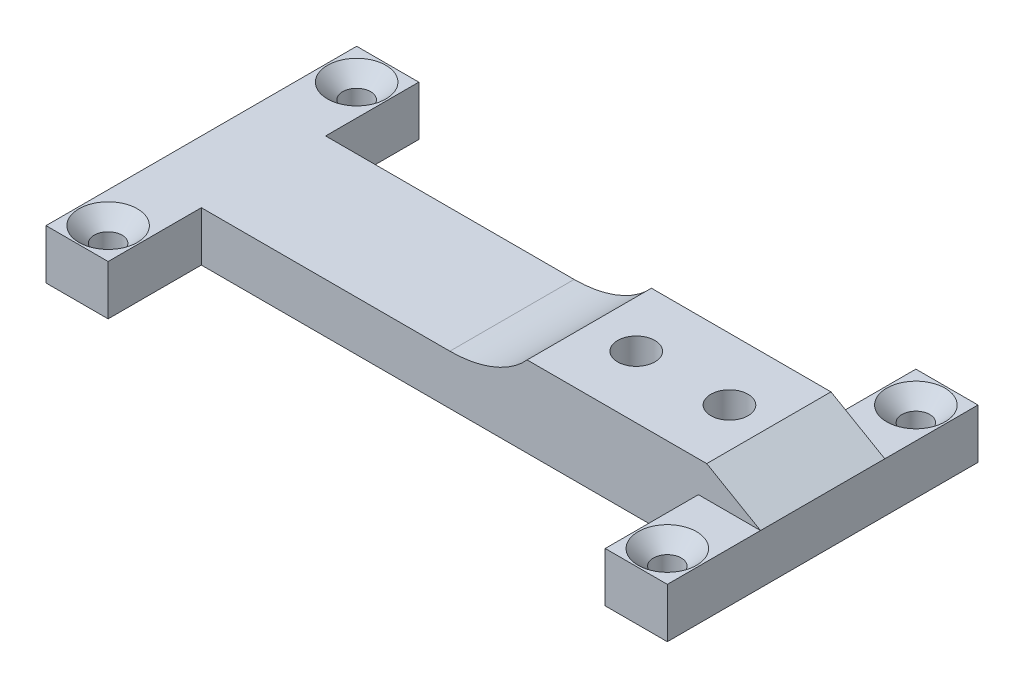
SolidWorks part; units mm, degrees
ref_plane "Front Plane" through (0, 0, 0) normal (0, 0, 1) x (1, 0, 0)
ref_plane "Top Plane" through (0, 0, 0) normal (0, 1, 0) x (1, 0, 0)
ref_plane "Right Plane" through (0, 0, 0) normal (1, 0, 0) x (0, 0, -1)
sketch "Sketch1" plane through (0, 0, 0) normal (0, 0, 1) x (1, 0, 0)
  line L0 (0, 0) -> (0, 6.35)
  line L1 (0, 6.35) -> (0, -6.35)
  line L2 (50, -11.35) -> (41.3397, -6.35)
  line L3 (0, -6.35) -> (40, -6.35)
  line L4 (0, -6.35) -> (0, 6.35)
  line L5 (0, 6.35) -> (40, 6.35)
  line L6 (40, -6.35) -> (40, 6.35)
  line L7 (0, -11.35) -> (50, -11.35)
  line L8 (0, -11.35) -> (0, -19.35)
  line L9 (0, -19.35) -> (50, -19.35)
  line L10 (50, -11.35) -> (50, -19.35)
  line L11 (40, -6.35) -> (41.3397, -6.35)
  line L12 (0, -19.35) -> (-50, -19.35)
  line L13 (0, -19.35) -> (0, -11.35)
  line L14 (0, -11.35) -> (-50, -11.35)
  line L15 (-50, -19.35) -> (-50, -11.35)
  ellipse E0 centre (0, 0) end of major axis (-15, 0) minor radius 11.35
  dimension "D1" = 6.35
  dimension "D2" = 12.7
  dimension "D3" = 40
  dimension "D4" = 50
  dimension "D5" = 8
  dimension "D6" = 22.7
  dimension "D7" = 30
  dimension "D8" = 50
  dimension "D10" = 30
extrude "Boss-Extrude1" add sketch "Sketch1" along normal blind 20 contours L15 L12 L8 L14 | L10 L7 L8 L9 | E0 L7 L2 L11 L3
sketch "Sketch2" plane through (0, -6.35, 0) normal (0, 1, 0) x (1, 0, 0)
  line L0 (0, 0) -> (-50, 0) construction
  line L1 (0, 0) -> (40, 0)
  line L2 (0, 0) -> (0, -20)
  line L4 (40, 0) -> (40, -20)
  line L5 (12.4327, -20) -> (41.3397, -20) construction
  circle A0 centre (35, -10) radius 3
  circle A1 centre (20, -10) radius 3
  dimension "D3" = 5
  dimension "D8" = 6
  dimension "D9" = 6
  dimension "D1" = 40
  dimension "D2" = 0
  dimension "D4" = 20
  dimension "D5" = 20
  dimension "D6" = 10
  dimension "D7" = 10
extrude "Cut-Extrude1" cut sketch "Sketch2" against normal blind 17 contours A1 | A0
sketch "Sketch3" plane through (0, -19.35, 0) normal (0, -1, 0) x (1, 0, 0)
  line L0 (20, 15.5) -> (35, 15.5)
  line L1 (20, 4.5) -> (35, 4.5)
  arc A0 (20, 15.5) -> (20, 4.5) centre (20, 10) ccw
  arc A1 (35, 4.5) -> (35, 15.5) centre (35, 10) ccw
  dimension "D1" = 5.5
extrude "Cut-Extrude2" cut sketch "Sketch3" against normal blind 4
sketch "Sketch4" plane through (0, -19.35, 0) normal (0, -1, 0) x (1, 0, 0)
  line L1 (-50, 20) -> (-40, 20)
  line L2 (-50, 20) -> (-50, 35)
  line L3 (-50, 35) -> (-40, 35)
  line L4 (-40, 20) -> (-40, 35)
  line L5 (50, 20) -> (40, 20)
  line L6 (50, 20) -> (50, 35)
  line L7 (50, 35) -> (40, 35)
  line L8 (40, 20) -> (40, 35)
  line L9 (-50, 0) -> (-40, 0)
  line L10 (-50, 0) -> (-50, -15)
  line L11 (-50, -15) -> (-40, -15)
  line L12 (-40, 0) -> (-40, -15)
  line L13 (50, 0) -> (40, 0)
  line L14 (50, 0) -> (50, -15)
  line L15 (50, -15) -> (40, -15)
  line L16 (40, 0) -> (40, -15)
  dimension "D1" = 15
  dimension "D2" = 15
  dimension "D3" = 10
  dimension "D4" = 10
  dimension "D5" = 15
  dimension "D6" = 15
extrude "Boss-Extrude2" add sketch "Sketch4" against normal blind 8
sketch "Sketch5" plane through (0, -11.35, 0) normal (0, 1, 0) x (1, 0, 0)
  point P25 (-45, 10)
  point P27 (-45, -30)
  point P29 (45, -30)
  point P31 (45, 10)
sketch "Sketch8" plane through (0, -11.35, 0) normal (0, 1, 0) x (1, 0, 0)
  point P0 (-45, 10)
  point P3 (-45, -30)
  point P6 (45, -30)
  point P9 (45, 10)
hole_wizard "CSK for M4 Flat Head Machine Screw1" positions "Sketch8" profile "Sketch7" countersink size "M4" standard "ANSI Metric" end condition through all
sketch "Sketch7" plane through (-45, -11.35, -10) normal (1, 0, 0) x (0, 0, 1)
  line L0 (0, 0) -> (0, 8)
  line L1 (0, 8) -> (2.25, 8)
  line L2 (2.25, 8) -> (2.25, 2.45)
  line L3 (2.25, 2.45) -> (4.7, 0)
  line L5 (4.7, 0) -> (0, 0)
  line L6 (-2.25, 2.45) -> (-4.7, 0) construction
  line L11 (0, -6.35) -> (0, 107.95) construction
  dimension "Thru Hole Dia." = 4.5
  dimension "Thru Hole Depth" = 8
  dimension "Near C'Sink Dia." = 9.4
  dimension "Near C'Sink Angle" = 90
